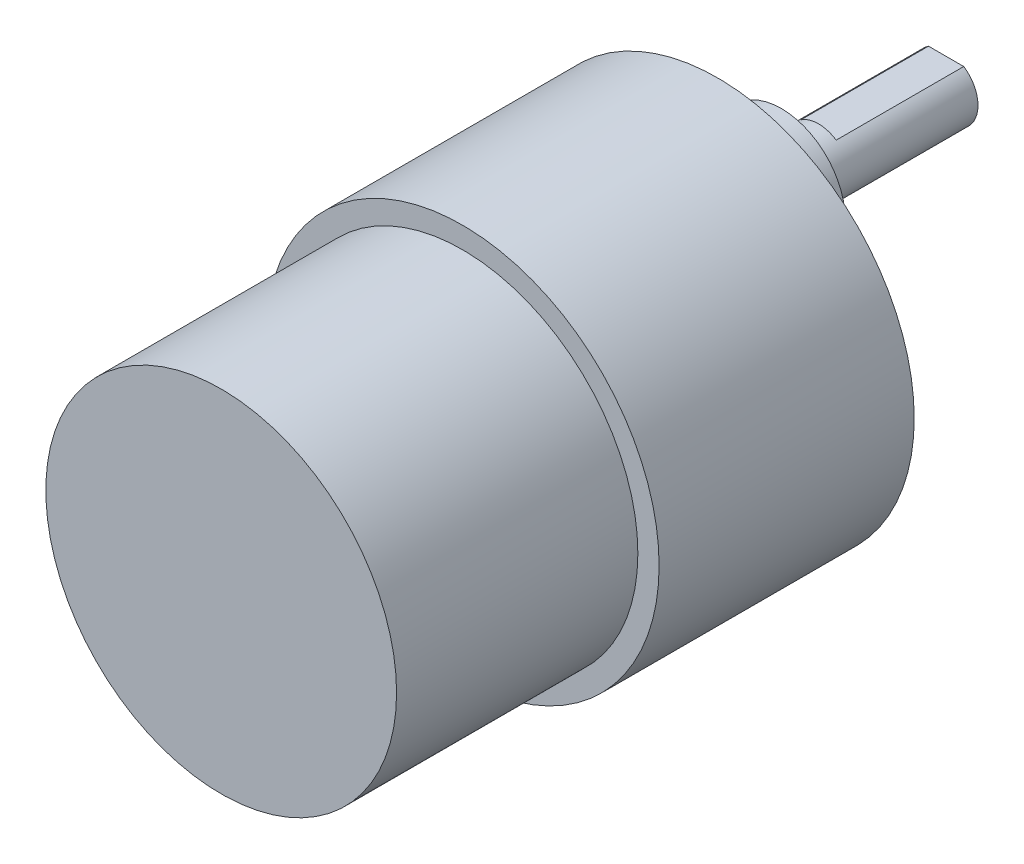
SolidWorks part; units mm, degrees
ref_plane "前视基准面" through (0, 0, 0) normal (0, 0, 1) x (1, 0, 0)
ref_plane "上视基准面" through (0, 0, 0) normal (0, 1, 0) x (1, 0, 0)
ref_plane "右视基准面" through (0, 0, 0) normal (1, 0, 0) x (0, 0, -1)
sketch "草图1" plane through (0, 0, 0) normal (0, 0, 1) x (1, 0, 0)
  circle A0 centre (0, 0) radius 18.5
  dimension "D1" = 37
extrude "凸台-拉伸1" add sketch "草图1" along normal blind 24
sketch "草图2" plane through (0, 0, 24) normal (0, 0, 1) x (1, 0, 0)
  circle A0 centre (0, 0) radius 16.5
  dimension "D1" = 33
extrude "凸台-拉伸2" add sketch "草图2" along normal blind 22.7
sketch "草图3" plane through (0, 0, 0) normal (0, 0, -1) x (-1, 0, 0)
  line L0 (-13.518, 7) -> (27.6104, 7) construction
  line L1 (0, 0) -> (0, 22.908) construction
  circle A0 centre (0, 7) radius 6
  dimension "D2" = 12
  dimension "D1" = 7
extrude "凸台-拉伸3" add sketch "草图3" along normal blind 6
sketch "草图4" plane through (0, 0, -6) normal (0, 0, -1) x (-1, 0, 0)
  circle A0 centre (0, 7) radius 3
  dimension "D1" = 6
extrude "凸台-拉伸4" add sketch "草图4" along normal blind 15.5
sketch "草图5" plane through (0, 0, -21.5) normal (0, 0, -1) x (-1, 0, 0)
  line L0 (0, 10) -> (0, 7) construction
  line L2 (-2.7491, 12.4225) -> (3.1949, 12.4225)
  line L3 (-2.7491, 12.4225) -> (-2.7491, 9.5)
  line L4 (-2.7491, 9.5) -> (3.1949, 9.5)
  line L5 (3.1949, 12.4225) -> (3.1949, 9.5)
  circle A0 centre (0, 7) radius 3 construction
  circle A1 centre (0, 7) radius 3 construction
  dimension "D1" = 2.5
extrude "切除-拉伸1" cut sketch "草图5" against normal blind 12
hole_wizard "M3 螺纹孔1" positions "草图6" profile "草图7" tap size "M3" standard "ISO"
sketch "草图6" plane through (0, 0, 0) normal (0, 0, -1) x (-1, 0, 0)
  line L0 (0, 18.5) -> (0, -18.5) construction
  line L1 (0, -18.5) -> (0, 0) construction
  line L2 (0, 0) -> (-18.5, 0) construction
  circle A0 centre (0, 0) radius 18.5 construction
  point P17 (-15.5, 0)
  point P27 (-7.75, 13.4234)
  point P28 (7.75, 13.4234)
  point P29 (15.5, 0)
  point P30 (7.75, -13.4234)
  point P31 (-7.75, -13.4234)
  point P33 (0, 0)
  dimension "D1" = 15.5
  dimension "D2" = 6
sketch "草图7" plane through (15.5, 0, 0) normal (1, 0, 0) x (0, 1, 0)
  line L0 (0, 0) -> (0, 8.2511)
  line L1 (0, 8.2511) -> (1.25, 7.5)
  line L2 (1.25, 7.5) -> (1.25, 0)
  line L5 (1.25, 0) -> (0, 0)
  line L10 (0, 8.2511) -> (-1.25, 7.5) construction
  line L11 (0, -6.35) -> (0, 107.95) construction
  dimension "螺纹孔钻头直径" = 2.5
  dimension "螺纹孔钻头深度" = 7.5
  dimension "导头角度" = 118
cosmetic thread "孔螺蚊线1" parameters "D1"=6, "D2"=3
cosmetic thread "孔螺蚊线2" parameters "D1"=6, "D2"=3
cosmetic thread "孔螺蚊线3" parameters "D1"=6, "D2"=3
cosmetic thread "孔螺蚊线4" parameters "D1"=6, "D2"=3
cosmetic thread "孔螺蚊线5" parameters "D1"=6, "D2"=3
cosmetic thread "孔螺蚊线6" parameters "D1"=6, "D2"=3
